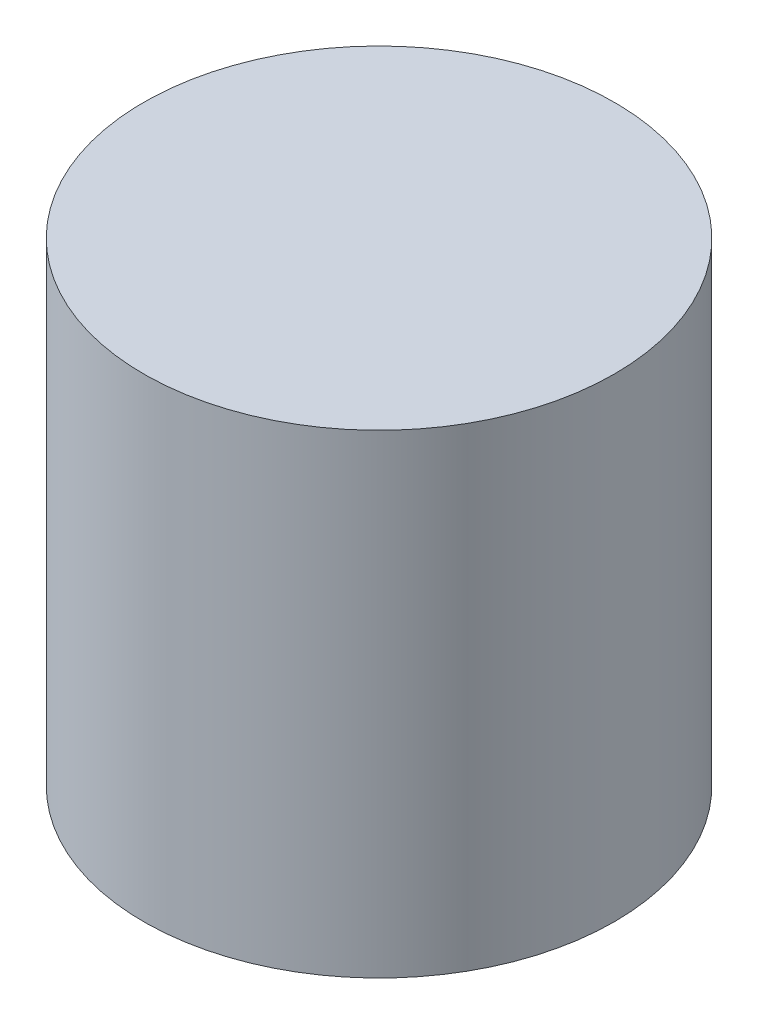
SolidWorks part; units mm, degrees
ref_plane "Front Plane" through (0, 0, 0) normal (0, 0, 1) x (1, 0, 0)
ref_plane "Top Plane" through (0, 0, 0) normal (0, 1, 0) x (1, 0, 0)
ref_plane "Right Plane" through (0, 0, 0) normal (1, 0, 0) x (0, 0, -1)
sketch "Sketch1" plane through (0, 0, 0) normal (0, 1, 0) x (1, 0, 0)
  circle A0 centre (0, 0) radius 12.7
extrude "Boss-Extrude1" add sketch "Sketch1" along normal up to surface (8.8 mm away) and the other way up to surface (16.8 mm away)
